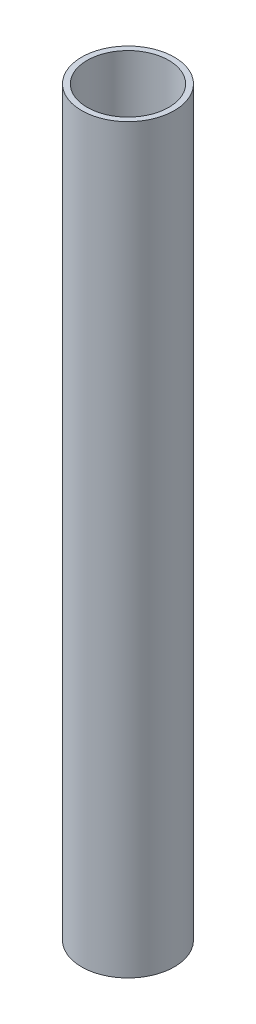
SolidWorks part; units mm, degrees
ref_plane "Front Plane" through (0, 0, 0) normal (0, 0, 1) x (1, 0, 0)
ref_plane "Top Plane" through (0, 0, 0) normal (0, 1, 0) x (1, 0, 0)
ref_plane "Right Plane" through (0, 0, 0) normal (1, 0, 0) x (0, 0, -1)
sketch "Sketch1" plane through (0, 0, 0) normal (0, 1, 0) x (1, 0, 0)
  circle A0 centre (0, 0) radius 12.7
  circle A1 centre (0, 0) radius 11.176
  dimension "D1" = 25.4
  dimension "D2" = 22.352
extrude "Boss-Extrude1" add sketch "Sketch1" along normal blind 203.2
